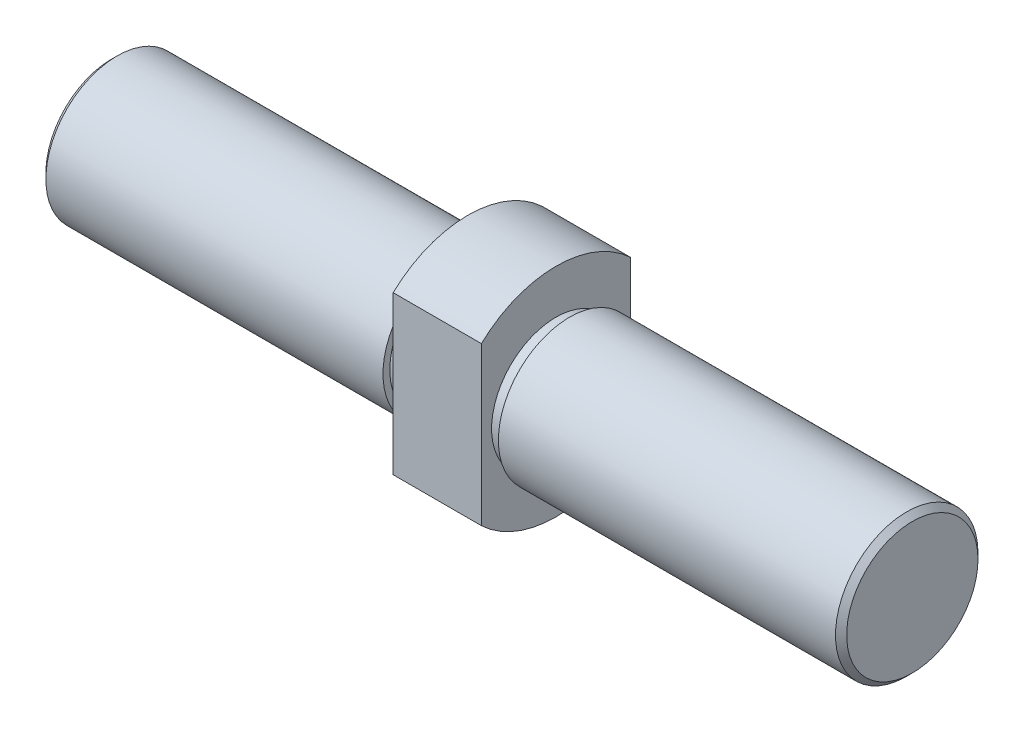
SolidWorks part; units mm, degrees
material "Сталь"
ref_plane "Спереди" through (0, 0, 0) normal (0, 0, 1) x (1, 0, 0)
ref_plane "Сверху" through (0, 0, 0) normal (0, 1, 0) x (1, 0, 0)
ref_plane "Справа" through (0, 0, 0) normal (1, 0, 0) x (0, 0, -1)
sketch "Эскиз1" plane through (0, 0, 0) normal (1, 0, 0) x (0, 0, -1)
  line L0 (22, 23.2379) -> (22, -23.2379)
  line L1 (-22, 23.2379) -> (-22, -23.2379)
  circle A0 centre (0, 0) radius 32
  dimension "D1" = 64
  dimension "D2" = 44
extrude "Бобышка-Вытянуть1" add sketch "Эскиз1" along normal blind 13 contours L0 A0 L1
sketch "Эскиз2" plane through (13, 0, 0) normal (1, 0, 0) x (0, 0, -1)
  circle A0 centre (0, 0) radius 19
  dimension "D1" = 38
extrude "Бобышка-Вытянуть2" add sketch "Эскиз2" along normal blind 105
sketch "Эскиз3" plane through (118, 0, 0) normal (1, 0, 0) x (0, 0, -1)
  circle A0 centre (0, 0) radius 21
  dimension "D1" = 42
extrude "Бобышка-Вытянуть3" add sketch "Эскиз3" against normal offset from surface (101 mm away) 4 up to face at (13, 0, 0)
cosmetic thread "Условное изображение резьбы1" parameters "D2"=38.704
chamfer "Фаска1" distance 1.648 angle 45 1 edges at (118, 0, -21)
mirror "Зеркальное отражение4" about plane through (0, 0, 0) normal (1, 0, 0) of bodies 107
